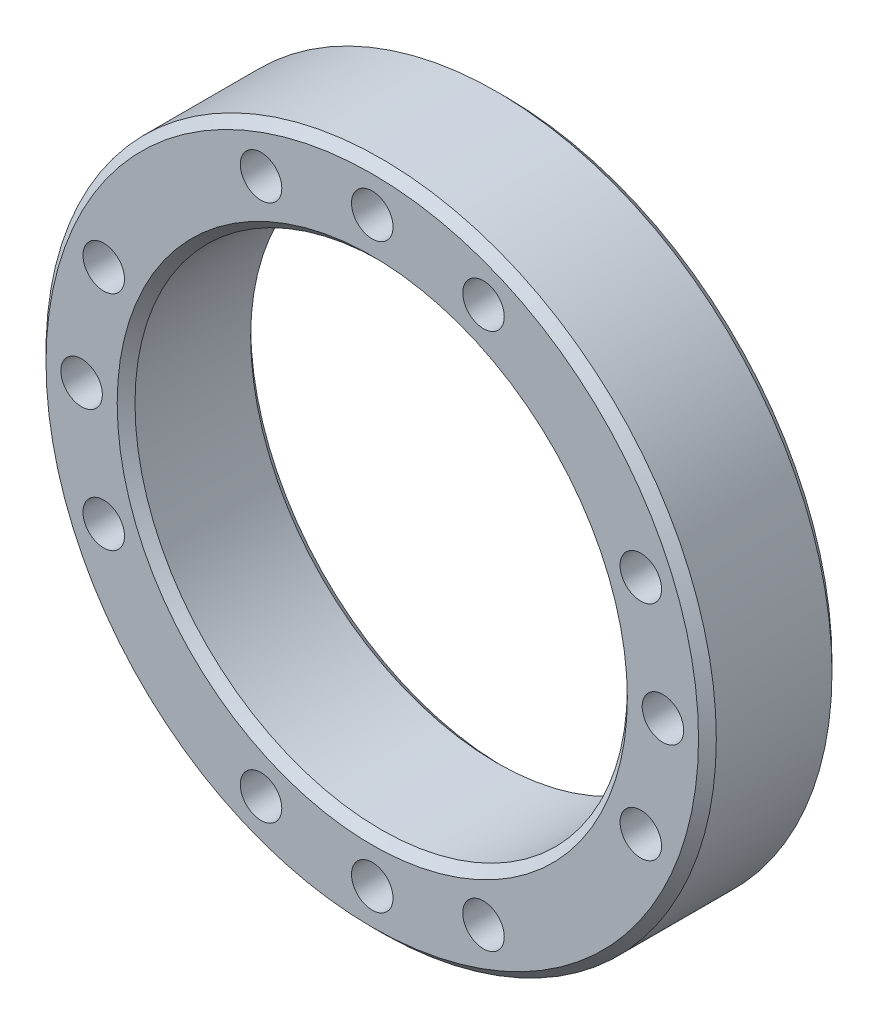
SolidWorks part; units mm, degrees
ref_plane "Front Plane" through (0, 0, 0) normal (0, 0, 1) x (1, 0, 0)
ref_plane "Top Plane" through (0, 0, 0) normal (0, 1, 0) x (1, 0, 0)
ref_plane "Right Plane" through (0, 0, 0) normal (1, 0, 0) x (0, 0, -1)
sketch "Sketch1" plane through (0, 0, 0) normal (0, 0, 1) x (1, 0, 0)
  circle A0 centre (0, 0) radius 113
  circle A1 centre (0, 0) radius 83
  dimension "D1" = 226
  dimension "D2" = 166
extrude "Boss-Extrude1" add sketch "Sketch1" along normal mid plane 45
cosmetic thread "Cosmetic Thread1" parameters "D2"=168
chamfer "Chamfer1" distance 3 angle 45 4 edges at (83, 0, -22.5) (83, 0, 22.5) (113, 0, -22.5) (113, 0, 22.5)
hole_wizard "M16x2.0 Tapped Hole1" positions "Sketch2" profile "Sketch3" tap size "M16x2.0" standard "ANSI Metric" end condition through all
sketch "Sketch2" plane through (0, 0, 22.5) normal (0, 0, 1) x (1, 0, 0)
  line L2 (0, 0) -> (37.503, 90.5402) construction
  line L4 (0, 0) -> (-37.503, 90.5402) construction
  line L6 (0, 0) -> (0, 113) construction
  line L7 (0, -83) -> (0, -113) construction
  circle A1 centre (0, 0) radius 113 construction
  circle A2 centre (0, 0) radius 98 construction
  circle A3 centre (0, 0) radius 83 construction
  circle A4 centre (0, 0) radius 113 construction
  circle A5 centre (0, 0) radius 98 construction
  point P0 (-37.503, 90.5402)
  point P4 (37.503, 90.5402)
  point P33 (0, 98)
  point P48 (0, -98)
  dimension "D3" = 196
  dimension "D4" = 196
  dimension "D1" = 22.5
  dimension "D2" = 22.5
sketch "Sketch3" plane through (-37.503, 90.5402, 22.5) normal (1, 0, 0) x (0, -1, 0)
  line L0 (0, 0) -> (0, 45)
  line L1 (0, 45) -> (7, 45)
  line L2 (7, 45) -> (7, 0)
  line L5 (7, 0) -> (0, 0)
  line L11 (0, -6.35) -> (0, 107.95) construction
  dimension "Thru Tap Drill Dia." = 14
  dimension "Thru Tap Drill Depth" = 45
cosmetic thread "Hole Thread1" parameters "D2"=16
cosmetic thread "Hole Thread2" parameters "D2"=16
cosmetic thread "Hole Thread3" parameters "D2"=16
pattern_circular "CirPattern1" count 4 over 360 about axis through (0, 0, 0) along (0, 0, 1) of "M16x2.0 Tapped Hole1"
